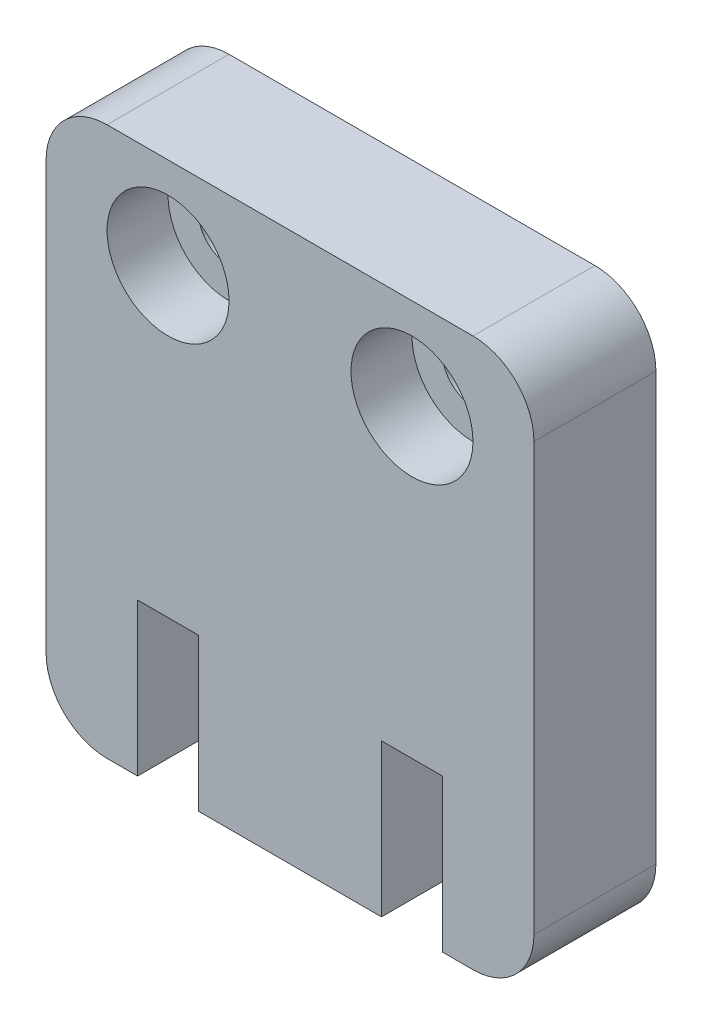
SolidWorks part; units mm, degrees
material "Acrylic (Medium-high impact)"
ref_plane "Front Plane" through (0, 0, 0) normal (0, 0, 1) x (1, 0, 0)
ref_plane "Top Plane" through (0, 0, 0) normal (0, 1, 0) x (1, 0, 0)
ref_plane "Right Plane" through (0, 0, 0) normal (1, 0, 0) x (0, 0, -1)
sketch "Model" plane through (0, 0, 0) normal (0, 0, 1) x (1, 0, 0)
  line L0 (2, 0) -> (3, 0)
  line L1 (3, 0) -> (3, 5)
  line L2 (3, 5) -> (5, 5)
  line L3 (5, 5) -> (5, 0)
  line L4 (5, 0) -> (11, 0)
  line L5 (11, 0) -> (11, 5)
  line L6 (11, 5) -> (13, 5)
  line L7 (13, 5) -> (13, 0)
  line L8 (13, 0) -> (14, 0)
  line L9 (0, 2) -> (0, 16)
  line L10 (2, 18) -> (14, 18)
  line L11 (16, 16) -> (16, 2)
  circle A0 centre (4, 15) radius 1
  circle A3 centre (12, 15) radius 1
  arc A4 (0, 16) -> (2, 18) centre (2, 16) cw
  arc A5 (2, 0) -> (0, 2) centre (2, 2) cw
  arc A6 (16, 2) -> (14, 0) centre (14, 2) cw
  arc A7 (14, 18) -> (16, 16) centre (14, 16) cw
  dimension "D2" = 2
  dimension "D3" = 16
  dimension "D4" = 13
  dimension "D7" = 3
  dimension "D11" = 2
  dimension "D5" = 6
  dimension "D6" = 2
  dimension "D8" = 4
  dimension "D9" = 4
  dimension "D10" = 5
other "AlignGroup1"
other "AlignGroup2"
other "AlignGroup3"
other "AlignGroup4"
other "AlignGroup5"
other "AlignGroup6"
other "AlignGroup7"
other "AlignGroup8"
extrude "Boss-Extrude1" add sketch "Model" along normal blind 4
sketch "Sketch2" plane through (0, 0, 4) normal (0, 0, 1) x (1, 0, 0)
  circle A0 centre (4, 15) radius 2
  circle A1 centre (12, 15) radius 2
extrude "Cut-Extrude1" cut sketch "Sketch2" against normal blind 2
